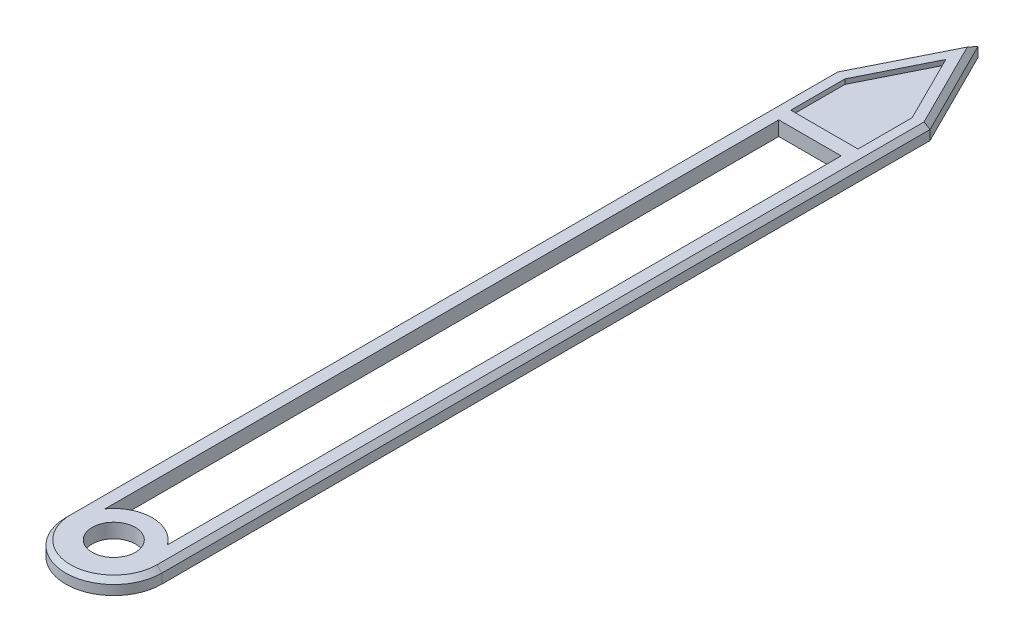
SolidWorks part; units mm, degrees
ref_plane "Front Plane" through (0, 0, 0) normal (0, 0, 1) x (1, 0, 0)
ref_plane "Top Plane" through (0, 0, 0) normal (0, 1, 0) x (1, 0, 0)
ref_plane "Right Plane" through (0, 0, 0) normal (1, 0, 0) x (0, 0, -1)
sketch "Sketch1" plane through (0, 0, 0) normal (0, 1, 0) x (1, 0, 0)
  line L0 (-1, 0) -> (1, 0) construction
  line L1 (-1, 0) -> (-1, 16)
  line L2 (0, 0) -> (0, 18) construction
  line L3 (1, 0) -> (1, 16)
  line L4 (-1, 16) -> (0, 18)
  line L5 (0, 18) -> (1, 16)
  line L6 (-0.65, 0.4664) -> (-0.65, 14.5)
  line L7 (-0.65, 14.5) -> (0.65, 14.5)
  line L8 (0.65, 14.5) -> (0.65, 0.4664)
  circle A0 centre (0, 0) radius 0.45
  arc A1 (-1, 0) -> (1, 0) centre (0, 0) ccw
  arc A2 (-0.65, 0.4664) -> (0.65, 0.4664) centre (0, 0) cw
  dimension "D1" = 0.9
  dimension "D4" = 0.35
  dimension "D2" = 2
  dimension "D3" = 16
  dimension "D5" = 3.5
  dimension "D6" = 0.35
  dimension "D7" = 18
extrude "Boss-Extrude1" add sketch "Sketch1" along normal blind 0.3
sketch "Sketch2" plane through (0, 0.3, 0) normal (0, 1, 0) x (1, 0, 0)
  line L7 (-0.7, 15.9292) -> (-0.7, 14.8)
  line L8 (-0.7, 14.8) -> (0.7, 14.8)
  line L9 (0.7317, 15.8658) -> (0, 17.3292)
  line L10 (0, 17.3292) -> (-0.7317, 15.8658)
  line L11 (0.7, 15.9292) -> (0, 17.3292)
  line L12 (0, 17.3292) -> (-0.7, 15.9292)
  line L13 (0.7, 14.8) -> (0.7, 15.9292)
  line L14 (0, 17.3292) -> (0, 14.8) construction
  line L15 (-1, 16) -> (-1, 0) construction
  line L16 (0.65, 14.5) -> (-0.65, 14.5) construction
  dimension "D2" = 0.3
  dimension "D3" = 0.3
  dimension "D1" = 0.3
extrude "Cut-Extrude1" cut sketch "Sketch2" against normal blind 0.1
chamfer "Chamfer1" distance 0.1 angle 45 5 edges at (-1, 0.3, -8) (0, 0.3, 1) (-0.5, 0.3, -17) (0.5, 0.3, -17) (1, 0.3, -8)
